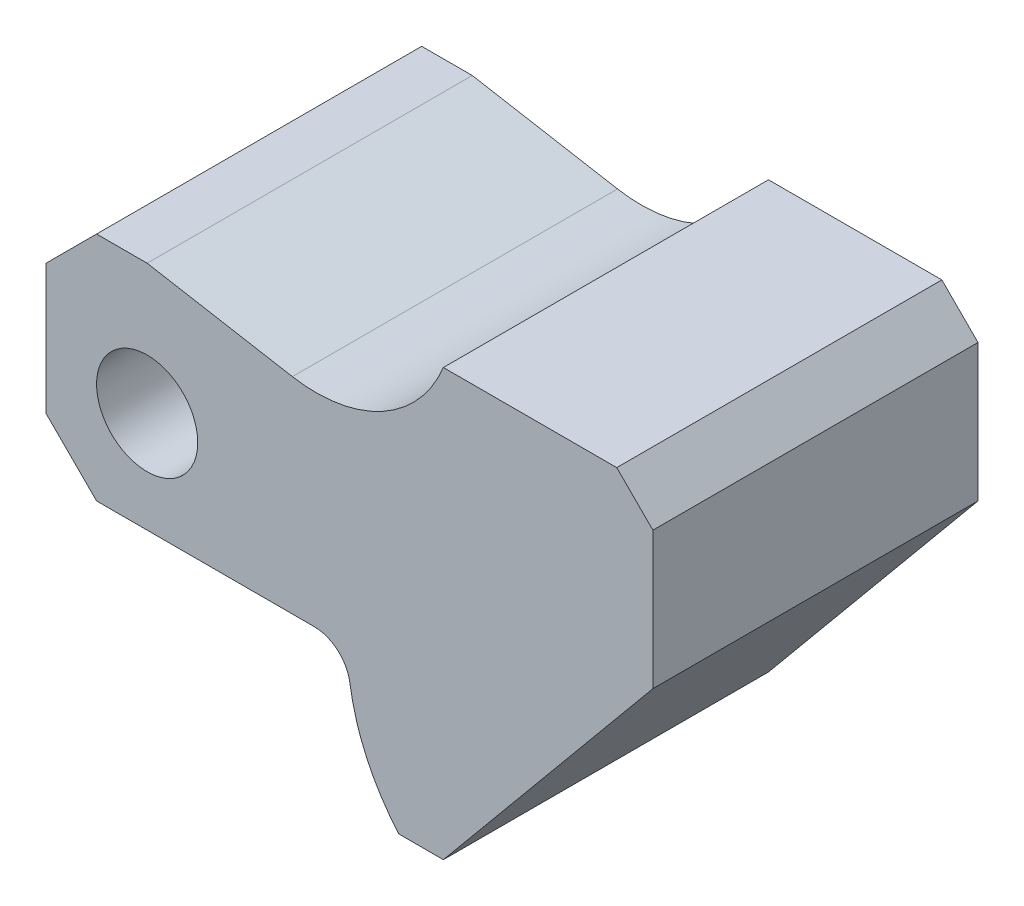
SolidWorks part; units mm, degrees
material "AISI 1020"
ref_plane "Plan de face" through (0, 0, 0) normal (0, 0, 1) x (1, 0, 0)
ref_plane "Plan de dessus" through (0, 0, 0) normal (0, 1, 0) x (1, 0, 0)
ref_plane "Plan de droite" through (0, 0, 0) normal (1, 0, 0) x (0, 0, -1)
sketch "Esquisse1" plane through (0, 0, 0) normal (0, 0, 1) x (1, 0, 0)
  line L0 (0, 0) -> (29, 35)
  line L1 (29, 35) -> (29, 54)
  line L2 (24, 59) -> (0, 59)
  line L3 (0, 0) -> (-6.166, 0)
  line L4 (-48, 19) -> (-17.8875, 19)
  line L5 (-55, 26) -> (-55, 44)
  line L6 (-48, 51) -> (-41, 51)
  line L7 (-41, 51) -> (-20.896, 47.4551)
  line L8 (-40.6165, 0) -> (-41, 0) construction
  line L9 (-41, 0) -> (-41, 89.6438) construction
  line L10 (-94.4879, 33) -> (3.1136, 33) construction
  line L11 (-55, 44) -> (-48, 51)
  line L12 (-48, 19) -> (-55, 26)
  line L13 (29, 54) -> (24, 59)
  arc A0 (-12.9418, 14.7353) -> (-6.166, 0) centre (15.7429, 19) ccw
  arc A1 (-12.9418, 14.7353) -> (-17.8875, 19) centre (-17.8875, 14) ccw
  arc A2 (-20.896, 47.4551) -> (0, 59) centre (-17.5966, 66.1665) ccw
  circle A3 centre (-41, 33) radius 7
  point P3 (15.7429, 19)
  point P4 (29, 59)
  point P8 (-55, 19)
  point P13 (-55, 51)
  dimension "D6" = 29
  dimension "D7" = 5
  dimension "D12" = 19
  dimension "D15" = 14
  dimension "D1" = 29
  dimension "D2" = 59
  dimension "D3" = 24
  dimension "D4" = 29
  dimension "D5" = 19
  dimension "D8" = 84
  dimension "D9" = 32
  dimension "D10" = 10
  dimension "D11" = 14
  dimension "D13" = 14
  dimension "D14" = 14
  dimension "D16" = 7
  dimension "D17" = 45
  dimension "D18" = 7
  dimension "D19" = 45
  dimension "D20" = 5
  dimension "D21" = 45
extrude "Boss.-Extru.1" add sketch "Esquisse1" against normal blind 45
